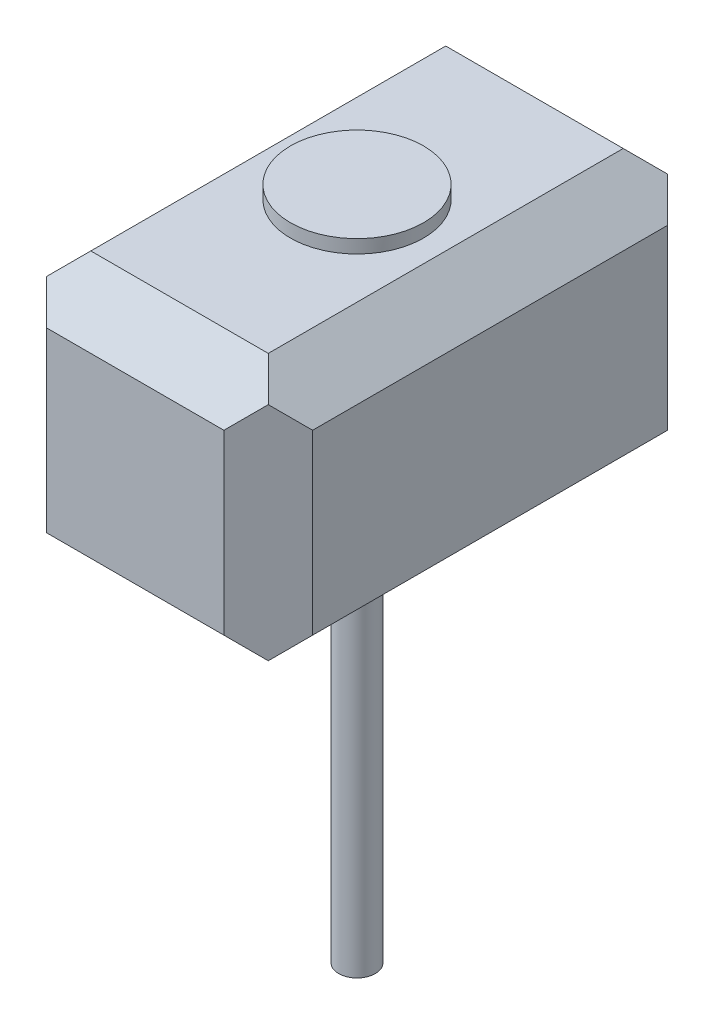
SolidWorks part; units mm, degrees
ref_plane "前视基准面" through (0, 0, 0) normal (0, 0, 1) x (1, 0, 0)
ref_plane "上视基准面" through (0, 0, 0) normal (0, 1, 0) x (1, 0, 0)
ref_plane "右视基准面" through (0, 0, 0) normal (1, 0, 0) x (0, 0, -1)
sketch "草图1" plane through (0, 0, 0) normal (0, 0, 1) x (1, 0, 0)
  line L1 (-30, 30) -> (30, 30)
  line L2 (-30, 30) -> (-30, -30)
  line L3 (-30, -30) -> (30, -30)
  line L4 (30, 30) -> (30, -30)
  line L5 (-30, 30) -> (30, -30) construction
  line L6 (-30, -30) -> (30, 30) construction
  point P0 (0, 0)
  dimension "D1" = 60
  dimension "D2" = 60
extrude "凸台-拉伸1" add sketch "草图1" along normal blind 100
chamfer "倒角1" distance 10 angle 45 1 edges at (0, 30, 0)
chamfer "倒角2" distance 10 angle 45 1 edges at (-30, -5, 0)
chamfer "倒角3" distance 10 angle 45 1 edges at (5, -30, 0)
chamfer "倒角4" distance 10 angle 45 1 edges at (30, 0, 0)
chamfer "倒角5" distance 10 angle 45 1 edges at (0, 30, 100)
chamfer "倒角6" distance 10 angle 45 1 edges at (30, -5, 100)
chamfer "倒角7" distance 10 angle 45 1 edges at (-30, -5, 100)
chamfer "倒角8" distance 10 angle 45 1 edges at (0, -30, 100)
sketch "草图4" plane through (0, 30, 0) normal (0, 1, 0) x (1, 0, 0)
  line L0 (30, -10) -> (-30, -10) construction
  circle A0 centre (0, -50) radius 15
  point P2 (0, -10)
  dimension "D2" = 30
  dimension "D1" = 40
extrude "凸台-拉伸2" add sketch "草图4" along normal blind 3
sketch "草图5" plane through (0, -30, 0) normal (0, -1, 0) x (1, 0, 0)
  line L0 (-30, 10) -> (30, 10) construction
  circle A0 centre (0, 50) radius 4.1304
  point P2 (0, 10)
  dimension "D1" = 40
extrude "凸台-拉伸3" add sketch "草图5" along normal blind 89
chamfer "倒角9" distance 10 angle 45 1 edges at (30, 30, 50)
chamfer "倒角10" distance 10 angle 45 1 edges at (-30, 30, 50)
chamfer "倒角11" distance 10 angle 45 1 edges at (30, -30, 50)
